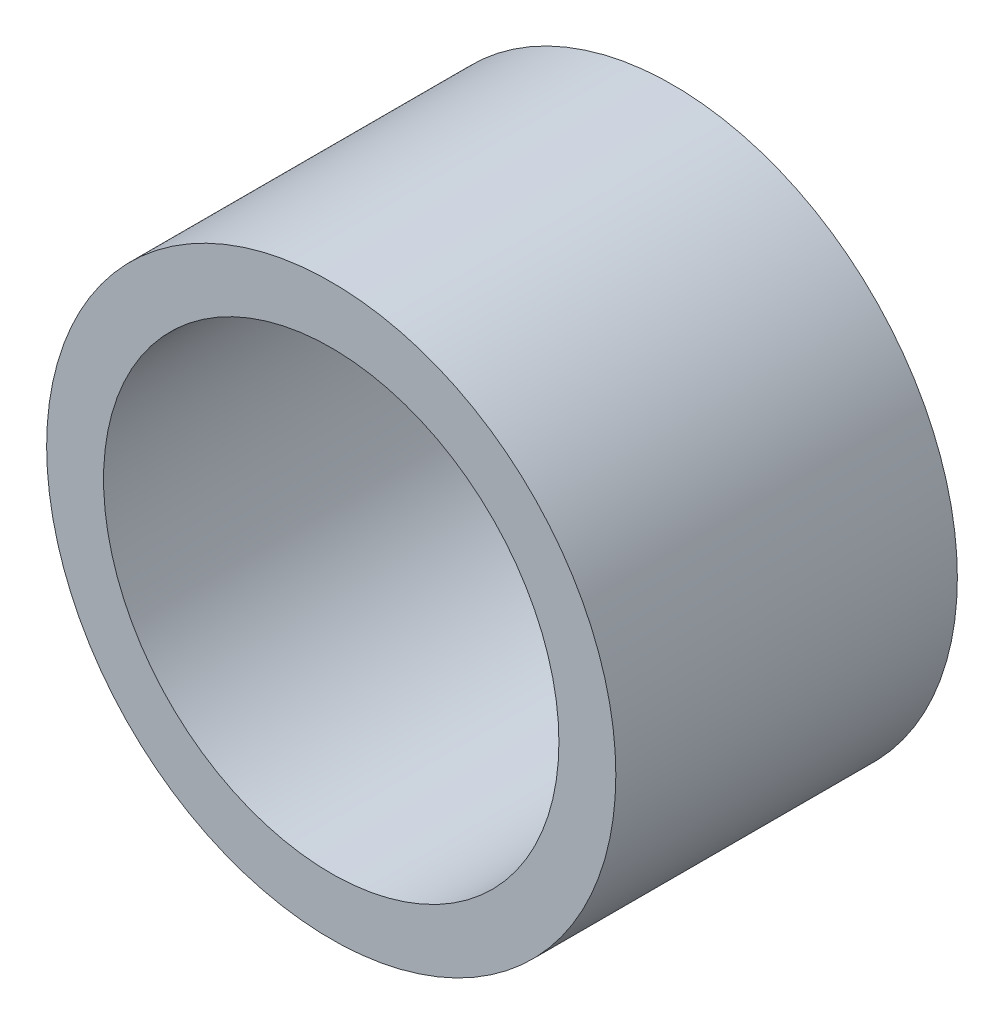
SolidWorks part; units mm, degrees
material "Nylon 101"
ref_plane "Front Plane" through (0, 0, 0) normal (0, 0, 1) x (1, 0, 0)
ref_plane "Top Plane" through (0, 0, 0) normal (0, 1, 0) x (1, 0, 0)
ref_plane "Right Plane" through (0, 0, 0) normal (1, 0, 0) x (0, 0, -1)
sketch "Sketch1" plane through (0, 0, 0) normal (0, 0, 1) x (1, 0, 0)
  circle A0 centre (0, 0) radius 7.9375
  circle A1 centre (0, 0) radius 6.35
  dimension "D1" = 15.875
  dimension "ID" = 12.7
extrude "Extrude1" add sketch "Sketch1" along normal mid plane 9.525
sketch "Sketch2" plane through (0, 0, 0) normal (1, 0, 0) x (0, 0, -1)
  line L0 (-4.7625, -6.35) -> (4.7625, -6.35) construction
  line L3 (4.7625, 6.35) -> (-4.7625, 6.35) construction
  line L5 (-4.7625, -6.35) -> (4.7625, -6.35)
  line L6 (4.7625, 6.35) -> (-4.7625, 6.35)
sketch "Sketch4" plane through (0, 0, 4.7625) normal (0, 0, 1) x (1, 0, 0)
  line L0 (0, 0) -> (-4.4901, 4.4901)
  line L1 (0, -3.4925) -> (0, 3.4925) construction
  circle A0 centre (0, 0) radius 6.35 construction
  dimension "D1" = 45
